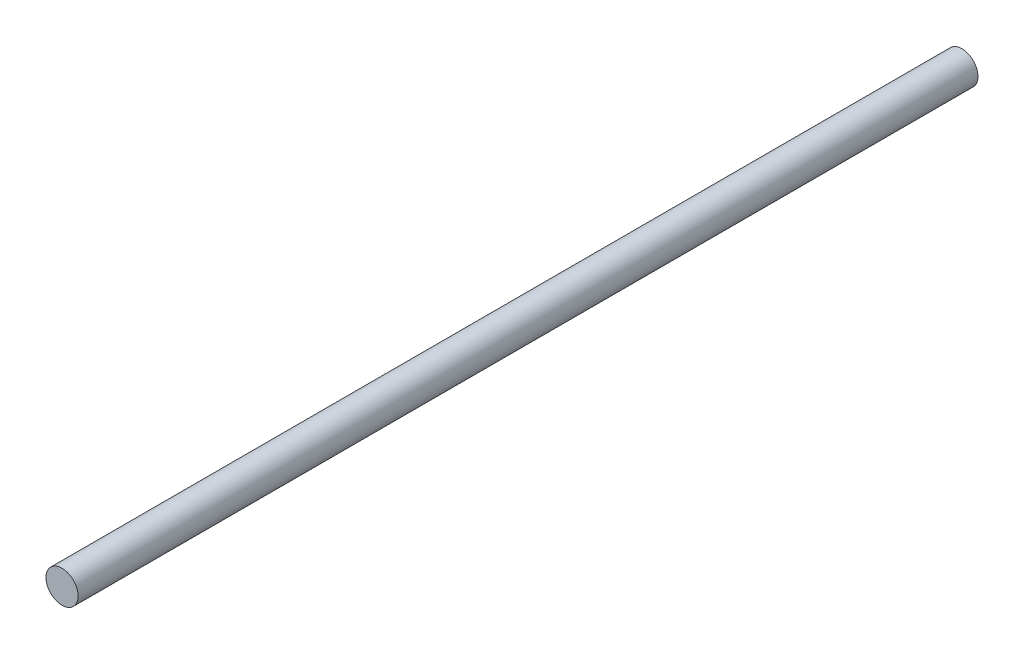
SolidWorks part; units mm, degrees
ref_plane "Front Plane" through (0, 0, 0) normal (0, 0, 1) x (1, 0, 0)
ref_plane "Top Plane" through (0, 0, 0) normal (0, 1, 0) x (1, 0, 0)
ref_plane "Right Plane" through (0, 0, 0) normal (1, 0, 0) x (0, 0, -1)
sketch "Sketch1" plane through (0, 0, 0) normal (0, 0, 1) x (1, 0, 0)
  circle A0 centre (0, 0) radius 5
  dimension "D1" = 10
extrude "Boss-Extrude1" add sketch "Sketch1" along normal blind 280
